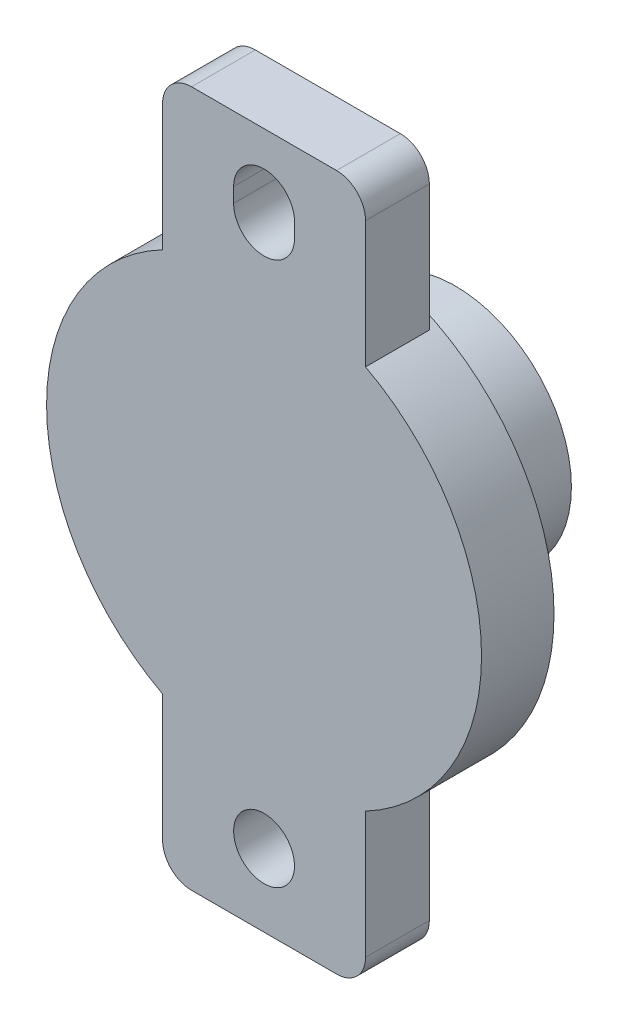
SolidWorks part; units mm, degrees
ref_plane "Front Plane" through (0, 0, 0) normal (0, 0, 1) x (1, 0, 0)
ref_plane "Top Plane" through (0, 0, 0) normal (0, 1, 0) x (1, 0, 0)
ref_plane "Right Plane" through (0, 0, 0) normal (1, 0, 0) x (0, 0, -1)
sketch "Sketch1" plane through (0, 0, 0) normal (0, 0, 1) x (1, 0, 0)
  line L0 (0, -55) -> (0, 55) construction
  line L1 (-3.5, 12) -> (3.5, 12)
  line L2 (-3.5, 12) -> (-3.5, 6.6332)
  line L3 (-3.5, -12) -> (3.5, -12)
  line L4 (3.5, 12) -> (3.5, 6.6332)
  line L5 (55, 0) -> (-55, 0) construction
  line L6 (-3.5, -6.6332) -> (-3.5, -12)
  line L7 (3.5, -6.6332) -> (3.5, -12)
  arc A0 (3.5, -6.6332) -> (3.5, 6.6332) centre (0, 0) ccw
  arc A1 (-3.5, 6.6332) -> (-3.5, -6.6332) centre (0, 0) ccw
  dimension "D1" = 15
  dimension "D2" = 24
  dimension "D3" = 7
  dimension "D4" = 3.5
  dimension "D5" = 12
extrude "Boss-Extrude1" add sketch "Sketch1" along normal blind 2.2
sketch "Sketch2" plane through (0, 0, 2.2) normal (0, 0, 1) x (1, 0, 0)
  circle A0 centre (0, 0) radius 7.5
  dimension "D1" = 15
extrude "Boss-Extrude2" add sketch "Sketch2" against normal blind 2.5
sketch "Sketch3" plane through (0, 0, 0) normal (0, 0, -1) x (-1, 0, 0)
  line L0 (0, 1.375) -> (0, -1.375) construction
  line L1 (3.5, -12) -> (-3.5, -12) construction
  circle A0 centre (0, -9.5) radius 1.05
  dimension "D1" = 2.1
  dimension "D2" = 2.5
extrude "Cut-Extrude1" cut sketch "Sketch3" against normal through all
sketch "Sketch4" plane through (0, 0, 0) normal (0, 0, -1) x (-1, 0, 0)
  line L0 (0, 9.7458) -> (0, 9.2458) construction
  line L1 (0, 1.375) -> (0, -1.375) construction
  line L2 (1.05, 9.7458) -> (1.05, 9.2458)
  line L3 (-1.05, 9.7458) -> (-1.05, 9.2458)
  line L4 (0, 10.7958) -> (5.1708, 10.7958) construction
  line L5 (0, 8.1958) -> (5.1708, 8.1958) construction
  line L6 (-3.5, 12) -> (3.5, 12) construction
  arc A0 (1.05, 9.7458) -> (-1.05, 9.7458) centre (0, 9.7458) ccw
  arc A1 (-1.05, 9.2458) -> (1.05, 9.2458) centre (0, 9.2458) ccw
  point P5 (0, 9.4958)
  dimension "D1" = 2.1
  dimension "D2" = 2.6
  dimension "D3" = 2.5042
extrude "Cut-Extrude2" cut sketch "Sketch4" against normal up to next
fillet "Fillet1" radius 1 4 edges at (3.5, -12, 1.1) (-3.5, -12, 1.1) (-3.5, 12, 1.1) (3.5, 12, 1.1)
ref_plane "Plane1" through (0, 0, -4.4) normal (0, 0, 1) x (1, 0, 0)
sketch "Sketch5" plane through (0, 0, -4.4) normal (0, 0, 1) x (1, 0, 0)
  circle A0 centre (0, 0) radius 4
  dimension "D1" = 8
extrude "Boss-Extrude3" add sketch "Sketch5" along normal blind 3.7 separate body
sketch "Sketch6" plane through (0, 0, -4.4) normal (0, 0, 1) x (1, 0, 0)
  line L0 (-1.2952, 1.25) -> (1.2952, 1.25)
  line L2 (-1.2952, -1.25) -> (1.2952, -1.25)
  line L3 (3.63, 0) -> (-3.63, 0) construction
  arc A0 (-1.2952, 1.25) -> (-1.2952, -1.25) centre (0, 0) ccw
  arc A1 (1.2952, -1.25) -> (1.2952, 1.25) centre (0, 0) ccw
  dimension "D1" = 1.25
  dimension "D3" = 1.8
  dimension "D2" = 2.5
extrude "Boss-Extrude4" add sketch "Sketch6" along normal up to surface (4.1 mm away) up to face at (7.5, 0, -0.3)
